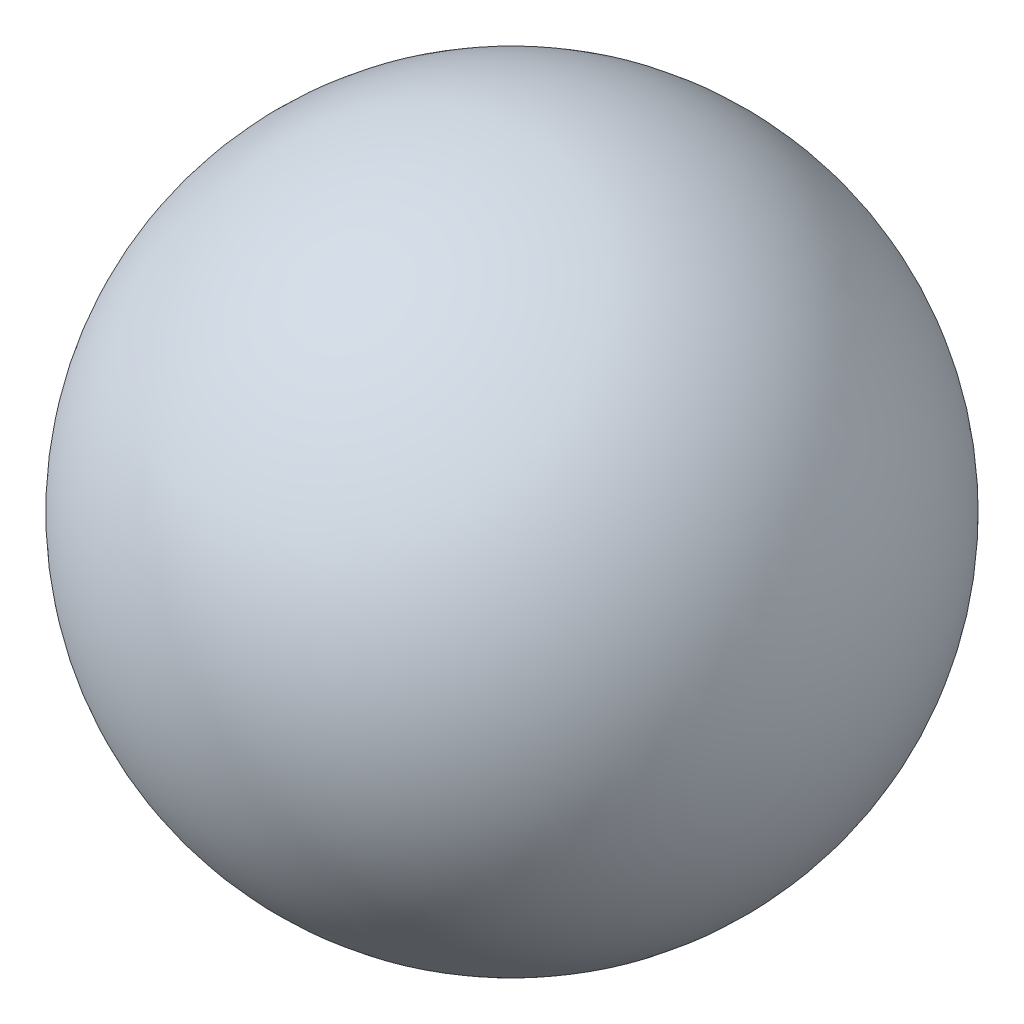
SolidWorks part; units mm, degrees
ref_plane "正面" through (0, 0, 0) normal (0, 0, 1) x (1, 0, 0)
ref_plane "平面" through (0, 0, 0) normal (0, 1, 0) x (1, 0, 0)
ref_plane "右側面" through (0, 0, 0) normal (1, 0, 0) x (0, 0, -1)
sketch "ｽｹｯﾁ1" plane through (0, 0, 0) normal (0, 0, 1) x (1, 0, 0)
  line L0 (0, 0) -> (0, 3.2548) construction
  line L1 (0, 2.5) -> (0, -2.5)
  arc A0 (0, -2.5) -> (0, 2.5) centre (0, 0) ccw
  dimension "D1" = 5
revolve "回転3" add sketch "ｽｹｯﾁ1" angle 360 about L0
